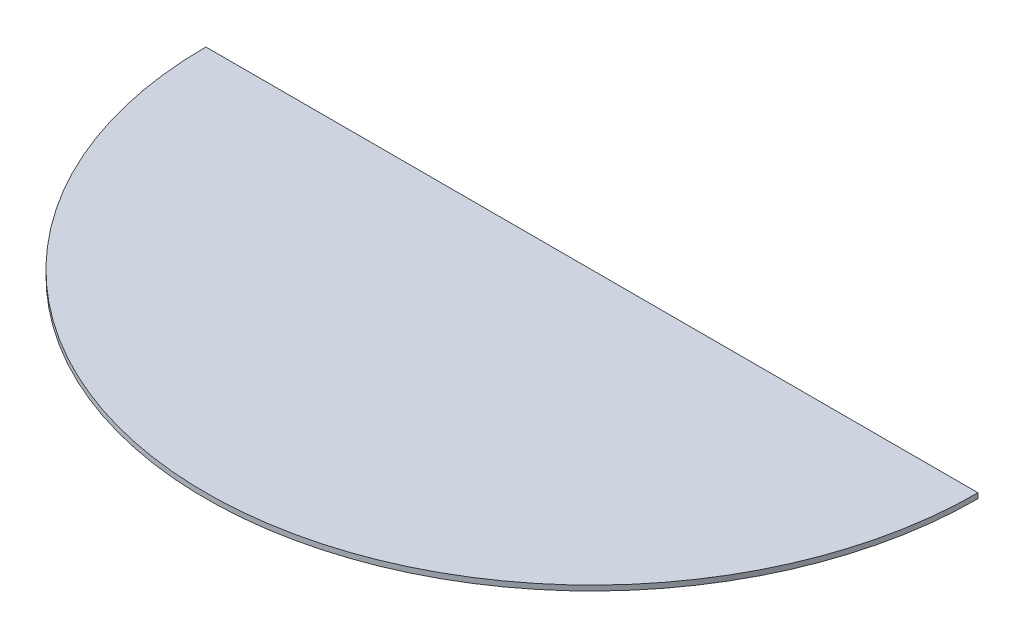
SolidWorks part; units mm, degrees
ref_plane "Ön Düzlem" through (0, 0, 0) normal (0, 0, 1) x (1, 0, 0)
ref_plane "Üst Düzlem" through (0, 0, 0) normal (0, 1, 0) x (1, 0, 0)
ref_plane "Sağ Düzlem" through (0, 0, 0) normal (1, 0, 0) x (0, 0, -1)
sketch "Sketch1" plane through (0, 0, 0) normal (0, 1, 0) x (1, 0, 0)
  line L0 (-75, 0) -> (75, 0)
  arc A0 (-75, 0) -> (75, 0) centre (0, 0) ccw
  dimension "D1" = 150
extrude "Boss-Extrude1" add sketch "Sketch1" along normal blind 1
